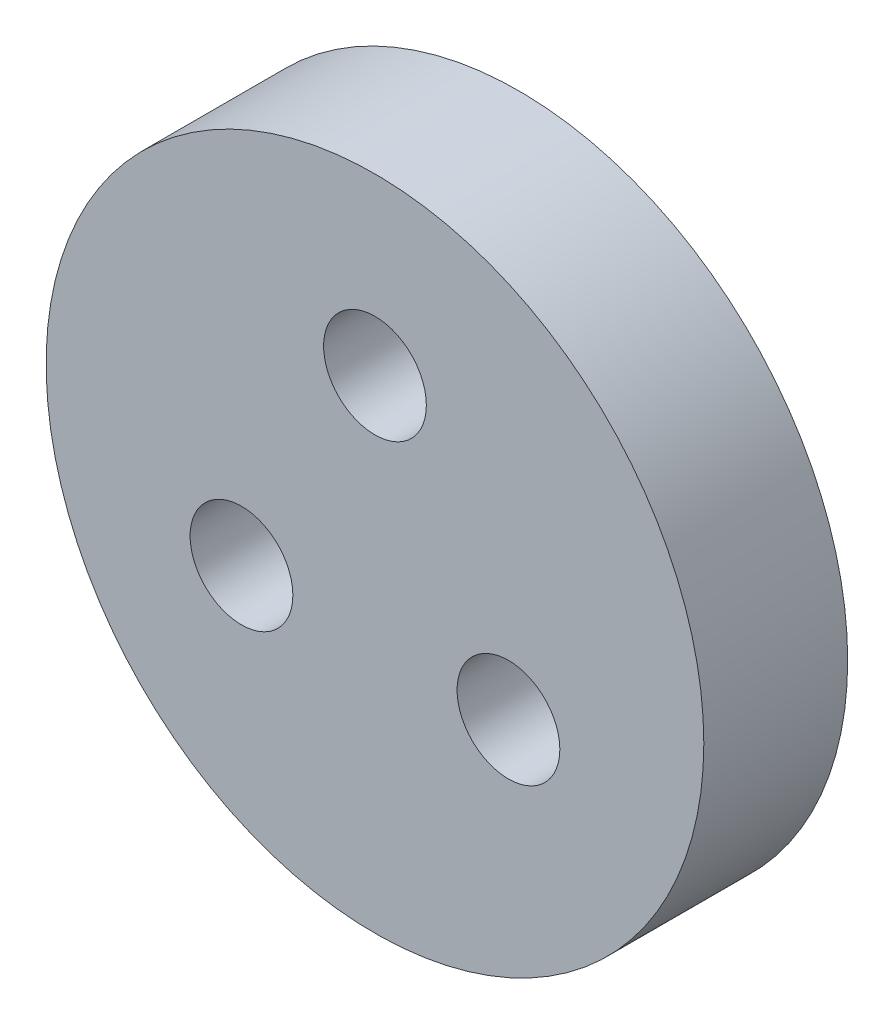
SolidWorks part; units mm, degrees
ref_plane "Front Plane" through (0, 0, 0) normal (0, 0, 1) x (1, 0, 0)
ref_plane "Top Plane" through (0, 0, 0) normal (0, 1, 0) x (1, 0, 0)
ref_plane "Right Plane" through (0, 0, 0) normal (1, 0, 0) x (0, 0, -1)
sketch "Sketch1" plane through (0, 0, 0) normal (0, 0, 1) x (1, 0, 0)
  circle A5 centre (-43.4831, -69.9891) radius 6
  circle A6 centre (-43.4831, -69.9891) radius 6
  circle A7 centre (-46.7307, -71.8641) radius 1.25
  circle A8 centre (-46.7307, -71.8641) radius 1.25
  circle A10 centre (-43.4831, -66.2391) radius 1.25
  circle A11 centre (-43.4831, -66.2391) radius 1.25
  circle A13 centre (-43.4831, -69.9891) radius 1.5
  circle A14 centre (-43.4831, -69.9891) radius 1.5
  circle A15 centre (-43.4831, -69.9891) radius 8
  circle A16 centre (-40.2355, -71.8641) radius 1.25
  circle A17 centre (-40.2355, -71.8641) radius 1.25
  dimension "D6" = 16
  dimension "D1" = 0
  dimension "D2" = 0
  dimension "D3" = 0
  dimension "D4" = 0
  dimension "D5" = 0
extrude "Boss-Extrude1" add sketch "Sketch1" along normal blind 3.5 contours A6 A15 | A15 A17 A8 A11 A14 | A14
sketch "Sketch2" plane through (0, 0, 0) normal (0, 0, -1) x (-1, 0, 0)
  circle A0 centre (43.4831, -69.9891) radius 1.5
  circle A1 centre (43.4831, -69.9891) radius 8 construction
  dimension "D1" = 0
  dimension "D2" = 3
extrude "Boss-Extrude2" add sketch "Sketch2" along normal blind 2
